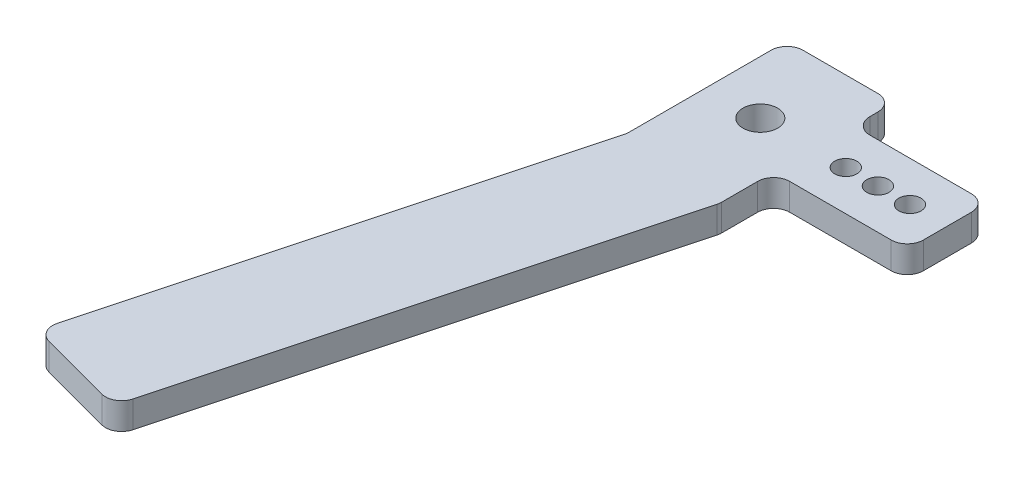
SolidWorks part; units mm, degrees
ref_plane "Front Plane" through (0, 0, 0) normal (0, 0, 1) x (1, 0, 0)
ref_plane "Top Plane" through (0, 0, 0) normal (0, 1, 0) x (1, 0, 0)
ref_plane "Right Plane" through (0, 0, 0) normal (1, 0, 0) x (0, 0, -1)
sketch "Sketch1" plane through (0, 0, 0) normal (0, 1, 0) x (1, 0, 0)
  line L0 (-30, 0) -> (-49.15, 0) construction
  line L1 (-30, -15) -> (30, -15) construction
  line L2 (-30, -15) -> (-30, 15) construction
  line L3 (-30, 15) -> (30, 15) construction
  line L4 (30, -15) -> (30, 15) construction
  line L5 (0, 15) -> (0, -15) construction
  line L6 (-30, 0) -> (30, 0) construction
  line L7 (-59.15, -15) -> (-82.4437, -101.9333)
  line L8 (-59.15, 15) -> (-39.15, 15)
  line L9 (-59.15, 15) -> (-59.15, -15)
  line L10 (-59.15, -15) -> (-39.15, -15) construction
  line L11 (-39.15, 15) -> (-39.15, -15)
  line L12 (-49.15, -15) -> (-49.15, 15) construction
  line L13 (-59.15, 0) -> (-39.15, 0) construction
  line L14 (-59.15, -15) -> (-39.8315, -20.1764) construction
  line L15 (-82.4437, -101.9333) -> (-63.1252, -107.1097)
  line L16 (-39.8315, -20.1764) -> (-63.1252, -107.1097)
  line L17 (-39.8315, -20.1764) -> (-39.15, -17.633)
  line L18 (-39.15, -15) -> (-39.15, -17.633)
  circle A0 centre (-49.15, 0) radius 3.25
  point P0 (0, 0)
  point P14 (-25, 15)
  dimension "D3" = 6.5
  dimension "D1" = 60
  dimension "D2" = 30
  dimension "D4" = 19.15
  dimension "D5" = 20
  dimension "D6" = 30
  dimension "D7" = 20
  dimension "D8" = 90
  dimension "D9" = 165
  dimension "D10" = 5
extrude "Boss-Extrude1" add sketch "Sketch1" along normal blind 5
sketch "Sketch2" plane through (0, 0, 0) normal (0, -1, 0) x (1, 0, 0)
  line L0 (-49.15, 0) -> (-26.65, 0) construction
  line L1 (-39.15, 17.633) -> (-39.15, -15) construction
  line L2 (-14.15, 7.5) -> (-39.15, 7.5)
  line L3 (-14.15, 7.5) -> (-14.15, -7.5)
  line L4 (-14.15, -7.5) -> (-39.15, -7.5)
  line L5 (-39.15, 7.5) -> (-39.15, -7.5)
  line L6 (-26.65, -7.5) -> (-26.65, 7.5) construction
  line L7 (-14.15, 0) -> (-39.15, 0) construction
  line L8 (-8.15, 7.5) -> (-33.15, 7.5)
  line L9 (-2.15, 7.5) -> (-27.15, 7.5)
  circle A0 centre (-33.15, 0) radius 2.075
  circle A1 centre (-49.15, 0) radius 3.25 construction
  circle A2 centre (-27.15, 0) radius 2.075
  circle A3 centre (-21.15, 0) radius 2.075
  line M7 (-39.15, -15) -> (-39.15, 17.633)
  dimension "D2" = 4.15
  dimension "D3" = 16
  dimension "D1" = 35
  dimension "D4" = 15
  dimension "D5" = 3
extrude "Boss-Extrude2" add sketch "Sketch2" against normal up to surface (5 mm away) contours L4 L3 L2 L8 A3 A2 A0 M7 up to face at (-57.0282, 5, 35.2793)
fillet "Fillet1" radius 3 10 edges at (-39.15, 2.5, 17.633) (-63.1252, 2.5, 107.1097) (-82.4437, 2.5, 101.9333) (-59.15, 2.5, 15) (-59.15, 2.5, -15) (-39.15, 2.5, -15) (-14.15, 2.5, -7.5) (-39.15, 2.5, -7.5) (-39.15, 2.5, 7.5) (-14.15, 2.5, 7.5)
